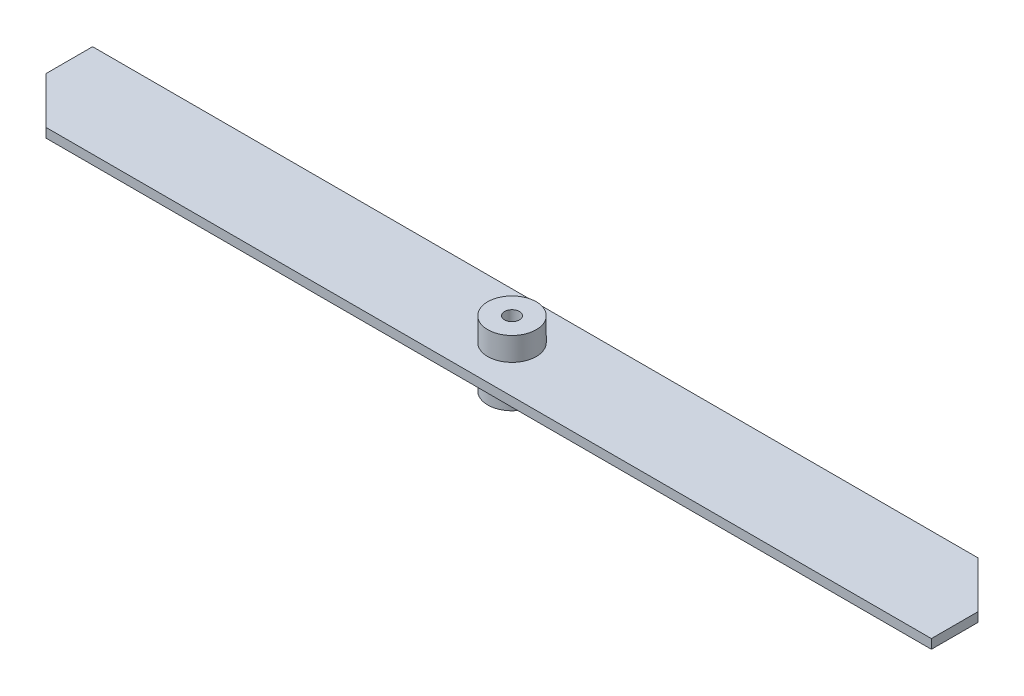
SolidWorks part; units mm, degrees
ref_plane "前视基准面" through (0, 0, 0) normal (0, 0, 1) x (1, 0, 0)
ref_plane "上视基准面" through (0, 0, 0) normal (0, 1, 0) x (1, 0, 0)
ref_plane "右视基准面" through (0, 0, 0) normal (1, 0, 0) x (0, 0, -1)
sketch "草图1" plane through (0, 0, 0) normal (0, 1, 0) x (1, 0, 0)
  line L0 (90, 10) -> (100, 0)
  line L1 (-90, -10) -> (100, -10)
  line L2 (-100, 0) -> (-100, 10)
  line L3 (-100, 10) -> (90, 10)
  line L4 (100, -10) -> (100, 0)
  line L5 (0, 10) -> (0, -10) construction
  line L6 (-100, 0) -> (100, 0) construction
  line L7 (-90, -10) -> (-100, 0)
  circle A0 centre (0, 0) radius 1.585
  point P0 (0, 0)
  point P1 (100, 10)
  point P2 (-100, -10)
  dimension "D1" = 200
  dimension "D2" = 20
extrude "凸台-拉伸1" add sketch "草图1" along normal blind 2
sketch "草图2" plane through (0, 0, 0) normal (0, -1, 0) x (1, 0, 0)
  circle A0 centre (0, 0) radius 5.2
extrude "凸台-拉伸2" add sketch "草图2" along normal mid plane 14
sketch "草图3" plane through (0, 7, 0) normal (0, 1, 0) x (1, 0, 0)
  circle A0 centre (0, 0) radius 1.585
extrude "切除-拉伸1" cut sketch "草图3" against normal blind 10
